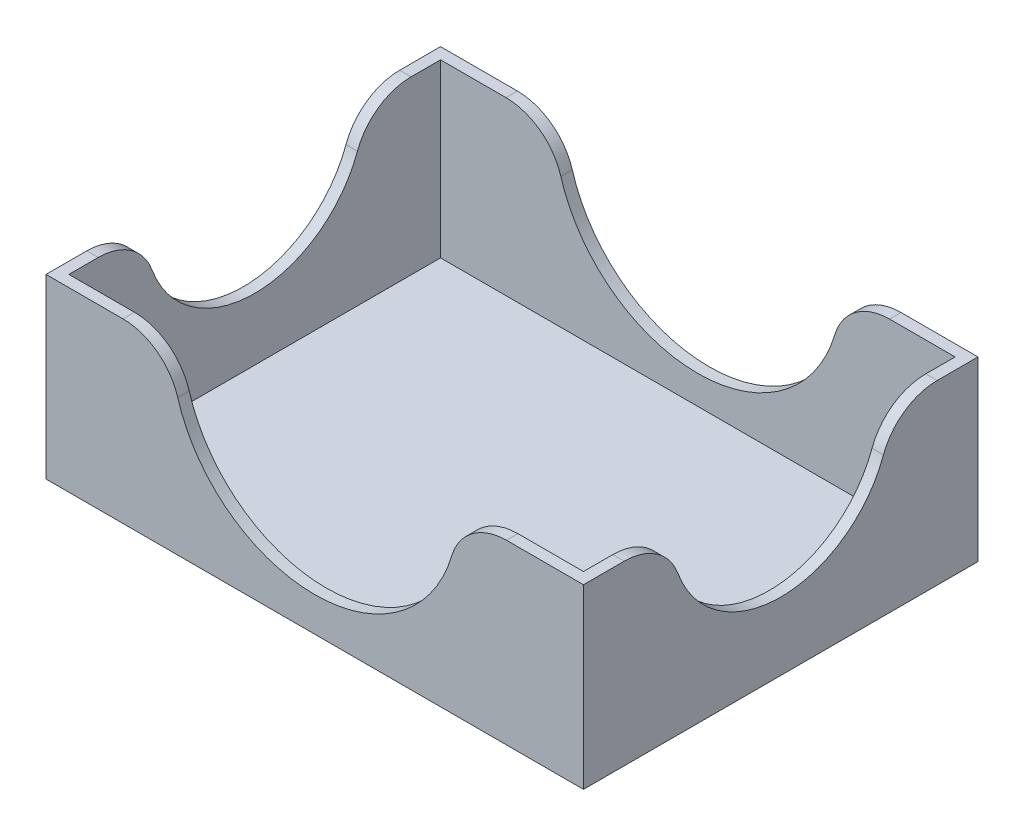
SolidWorks part; units mm, degrees
ref_plane "Front Plane" through (0, 0, 0) normal (0, 0, 1) x (1, 0, 0)
ref_plane "Top Plane" through (0, 0, 0) normal (0, 1, 0) x (1, 0, 0)
ref_plane "Right Plane" through (0, 0, 0) normal (1, 0, 0) x (0, 0, -1)
sketch "Sketch3" plane through (0, 0, 0) normal (0, 1, 0) x (1, 0, 0)
  line L1 (-45, 27.874) -> (45, 27.874)
  line L2 (-45, 27.874) -> (-45, -37.126)
  line L3 (-45, -37.126) -> (45, -37.126)
  line L4 (45, 27.874) -> (45, -37.126)
  line L5 (0, -37.126) -> (0, 27.874) construction
  line L6 (-45, -4.626) -> (45, -4.626) construction
  line L7 (-47, 29.874) -> (47, 29.874)
  line L8 (-47, 29.874) -> (-47, -39.126)
  line L9 (-47, -39.126) -> (47, -39.126)
  line L10 (47, 29.874) -> (47, -39.126)
  line L11 (0, -39.126) -> (0, 29.874) construction
  line L12 (-47, -4.626) -> (47, -4.626) construction
  point P202 (0, -4.626)
  point P276 (0, -4.626)
  dimension "D1" = 90
  dimension "D2" = 65
  dimension "D3" = 2
  dimension "D4" = 2
  dimension "D5" = 2
  dimension "D6" = 2
extrude "Boss-Extrude3" add sketch "Sketch3" along normal blind 30
sketch "Sketch4" plane through (0, 0, 0) normal (0, -1, 0) x (1, 0, 0)
  line L1 (-47, 39.126) -> (47, 39.126)
  line L2 (-47, 39.126) -> (-47, -29.874)
  line L3 (-47, -29.874) -> (47, -29.874)
  line L4 (47, 39.126) -> (47, -29.874)
  line L5 (0, -29.874) -> (0, 39.126) construction
  line L6 (-47, 4.626) -> (47, 4.626) construction
  point P116 (0, 4.626)
extrude "Boss-Extrude4" add sketch "Sketch4" along normal blind 1
sketch "Sketch5" plane through (47, 0, 0) normal (1, 0, 0) x (0, 0, -1)
  line L0 (-39.126, 30) -> (29.874, 30) construction
  circle A0 centre (-4.626, 30) radius 19.1299
  dimension "D1" = 38.2599
extrude "Cut-Extrude1" cut sketch "Sketch5" against normal through all both and the other way through all
fillet "Fillet1" radius 10 4 edges at (-46, 30, 23.7559) (-46, 30, -14.5039) (46, 30, -14.5039) (46, 30, 23.7559)
sketch "Sketch6" plane through (0, 0, -29.874) normal (0, 0, -1) x (-1, 0, 0)
  line L0 (-47, 30) -> (47, 30) construction
  circle A0 centre (0, 30) radius 25
  dimension "D1" = 50
extrude "Cut-Extrude2" cut sketch "Sketch6" against normal through all both
fillet "Fillet2" radius 10 4 edges at (25, 30, 38.126) (-25, 30, 38.126) (25, 30, -28.874) (-25, 30, -28.874)
